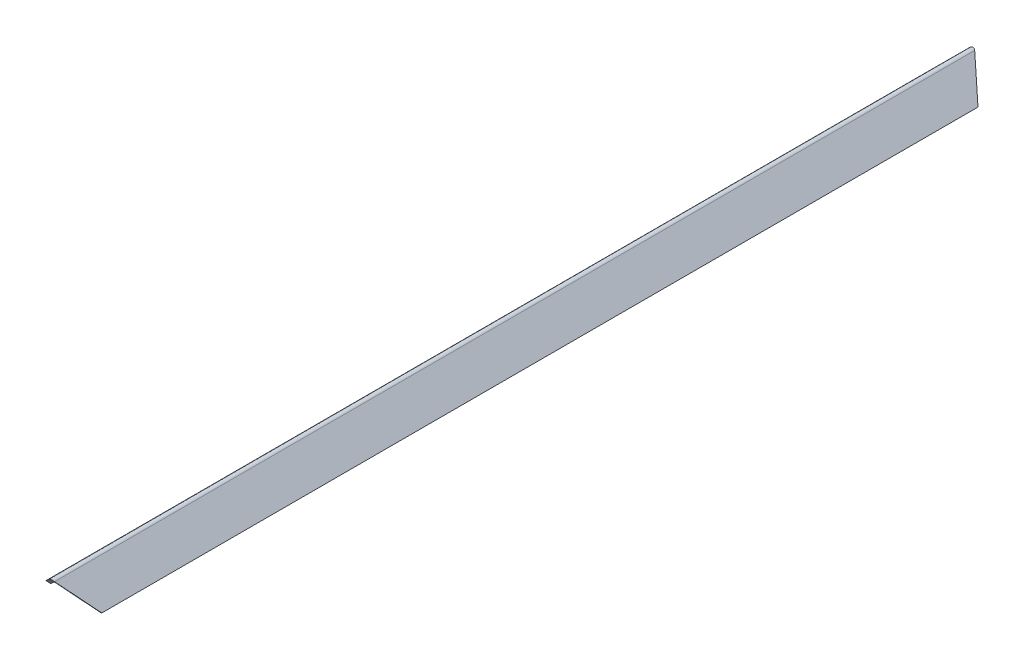
SolidWorks part; units mm, degrees
material "ASTM A36 Steel"
ref_plane "Front Plane" through (0, 0, 0) normal (0, 0, 1) x (1, 0, 0)
ref_plane "Top Plane" through (0, 0, 0) normal (0, 1, 0) x (1, 0, 0)
ref_plane "Right Plane" through (0, 0, 0) normal (1, 0, 0) x (0, 0, -1)
sketch "Sketch1" plane through (0, 0, 0) normal (0, 0, 1) x (1, 0, 0)
  line L1 (-43.8795, -42.2312) -> (-48.3599, -37.7314)
  line L4 (50.4577, -37.9452) -> (45.9579, -42.4256)
  line L6 (-43.8795, -42.2312) -> (-0.7246, 0.8545)
  line L7 (45.9579, -42.4256) -> (2.8699, 0.8492)
  line L8 (-48.3599, -37.7314) -> (-3.3615, 7.0726)
  line L9 (50.4577, -37.9452) -> (5.6537, 7.0531)
  arc A0 (-0.7246, 0.8545) -> (2.8699, 0.8492) centre (1.07, -0.943) cw
  arc A1 (5.6537, 7.0531) -> (-3.3615, 7.0726) centre (1.1363, 2.5553) ccw
  point P2 (1.1501, 8.93)
  dimension "D2" = 6.35
  dimension "D4" = 6.3747
  dimension "D5" = 3.4982
  dimension "D3" = 2.54
  dimension "D1" = 6.35
  dimension "D6" = 63.5
extrude "Boss-Extrude1" add sketch "Sketch1" along normal blind 1631.95
ref_plane "Plane1" through (-0.0916, -42.326, 0) normal (0.0022, 1, 0) x (1, -0.0022, 0)
sketch "Sketch3" plane through (1.8658, 1.8577, 0) normal (-0.7086, -0.7056, 0) x (0, 0, 1)
  line L0 (1631.95, -62.491) -> (0, -62.491) construction
  line L1 (1631.95, -1.4232) -> (1631.95, -62.491) construction
  line L2 (0, -1.4232) -> (0, -62.491) construction
  point P0 (1587.5, -62.491)
  point P5 (44.45, -62.491)
  dimension "D1" = 44.45
  dimension "D2" = 44.45
sketch "Sketch4" plane through (-0.789, 0.7903, 0) normal (0.7065, -0.7077, 0) x (0.7077, 0.7065, 0)
  line L0 (-60.8904, 1631.95) -> (-60.8904, 0) construction
  line L1 (-60.8904, 1631.95) -> (0.091, 1631.95) construction
  line L3 (-60.8904, 0) -> (0.091, 0) construction
  point P0 (-60.8904, 1587.5)
  point P1 (-60.8904, 44.45)
  dimension "D1" = 44.45
  dimension "D2" = 44.45
sketch "Sketch5" plane through (0, 0, 1631.95) normal (0, 0, 1) x (1, 0, 0)
  arc A0 (5.6537, 7.0531) -> (-3.3615, 7.0726) centre (1.1363, 2.5553) ccw construction
  point P0 (1.1501, 8.93)
sketch "Sketch6" plane through (0, 0, 0) normal (0, 0, -1) x (-1, 0, 0)
  point P0 (-1.1501, 8.93)
ref_plane "Plane3" through (-1.7396, -803.922, 927.063) normal (-0.0014, -0.6551, 0.7555) x (1, -0.0009, 0.0011)
sketch "Sketch10" plane through (-1.7396, -803.922, 927.063) normal (-0.0014, -0.6551, 0.7555) x (1, -0.0009, 0.0011)
  line L0 (-72.388, 958.2969) -> (-72.388, 1089.3501)
  line L1 (-72.388, 1089.3501) -> (76.0197, 1091.9386)
  line L2 (76.0197, 1091.9386) -> (76.0197, 958.2969)
  line L3 (76.0197, 958.2969) -> (-72.388, 958.2969)
extrude "Cut-Extrude2" cut sketch "Sketch10" along normal blind 76.2
ref_plane "Plane4" through (0.0083, 3.834, 4.4213) normal (0.0014, 0.6551, 0.7555) x (1, -0.0009, -0.0011)
sketch "Sketch11" plane through (0.0083, 3.834, 4.4213) normal (0.0014, 0.6551, 0.7555) x (1, -0.0009, -0.0011)
  line L0 (52.1907, -102.7815) -> (52.1907, 54.8309)
  line L1 (52.1907, 54.8309) -> (-64.5583, 54.8309)
  line L2 (-64.5583, 54.8309) -> (-64.5583, -102.7815)
  line L3 (-64.5583, -102.7815) -> (52.1907, -102.7815)
extrude "Cut-Extrude3" cut sketch "Sketch11" against normal blind 76.2
